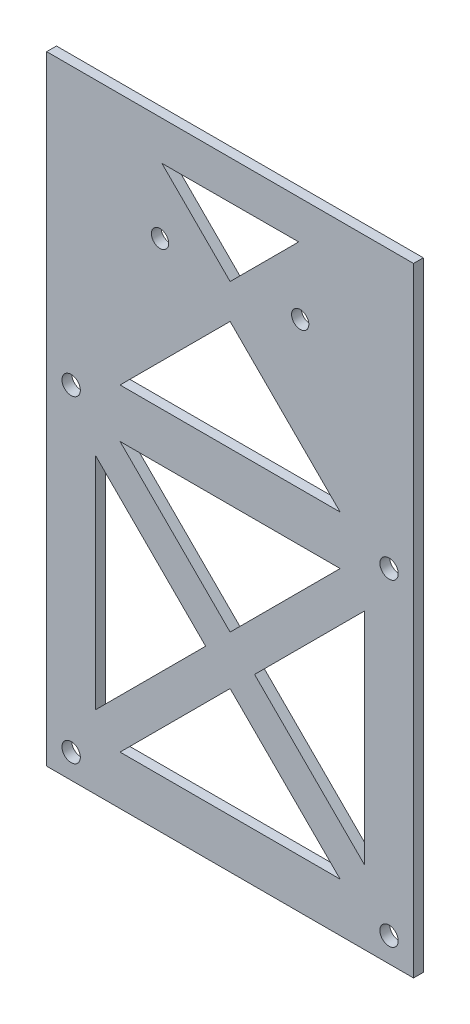
SolidWorks part; units mm, degrees
ref_plane "Front Plane" through (0, 0, 0) normal (0, 0, 1) x (1, 0, 0)
ref_plane "Top Plane" through (0, 0, 0) normal (0, 1, 0) x (1, 0, 0)
ref_plane "Right Plane" through (0, 0, 0) normal (1, 0, 0) x (0, 0, -1)
sketch "Sketch1" plane through (0, 0, 0) normal (0, 0, 1) x (1, 0, 0)
  line L2 (-37.5, -138.0294) -> (37.5, -138.0294)
  line L6 (-37.5, -264.5484) -> (37.5, -264.5484)
  line L7 (-27.5, -204.5484) -> (-27.5, -249.5484)
  line L8 (37.5, -264.5484) -> (37.5, -138.0294)
  line L9 (-37.5, -264.5484) -> (-37.5, -138.0294)
  line L11 (-22.5, -254.5484) -> (22.5, -254.5484)
  line L12 (27.5, -249.5484) -> (27.5, -204.5484)
  line L14 (-22.5, -199.5484) -> (22.5, -199.5484)
  line L19 (-27.5, -249.5484) -> (-5, -227.0484)
  line L20 (27.5, -204.5484) -> (5, -227.0484)
  line L21 (-27.5, -204.5484) -> (-5, -227.0484)
  line L22 (-22.5, -199.5484) -> (0, -222.0484)
  line L23 (0, -222.0484) -> (22.5, -199.5484)
  line L24 (0, -232.0484) -> (22.5, -254.5484)
  line L25 (5, -227.0484) -> (27.5, -249.5484)
  line L26 (-22.5, -189.5484) -> (22.5, -189.5484)
  line L27 (0, -232.0484) -> (-22.5, -254.5484)
  line L32 (0, -167.0484) -> (22.5, -189.5484)
  line L34 (0, -167.0484) -> (-22.5, -189.5484)
  line L35 (14.0243, -145.954) -> (0, -159.9784)
  line L37 (0, -159.9784) -> (-13.9583, -146.0201)
  line L38 (-13.9583, -146.0201) -> (14.0243, -145.954)
  circle A0 centre (32.5, -259.5484) radius 1.875
  circle A1 centre (-32.5, -259.5484) radius 1.875
  circle A2 centre (-32.5, -194.5484) radius 1.875
  circle A3 centre (32.5, -194.5484) radius 1.875
  circle A4 centre (14.3295, -159.5294) radius 1.765
  circle A5 centre (-14.3295, -159.5294) radius 1.765
  point P30 (0, -227.0484)
  dimension "D3" = 3.75
  dimension "D14" = 3.53
  dimension "D2" = 10
  dimension "D4" = 5
  dimension "D5" = 5
  dimension "D6" = 10
  dimension "D8" = 10
  dimension "D10" = 10
  dimension "D12" = 90
  dimension "D19" = 21.5
  dimension "D20" = 15
  dimension "D21" = 15
  dimension "D22" = 37.5
  dimension "D24" = 90
  dimension "D27" = 37.5
extrude "Boss-Extrude2" add sketch "Sketch1" along normal blind 2
